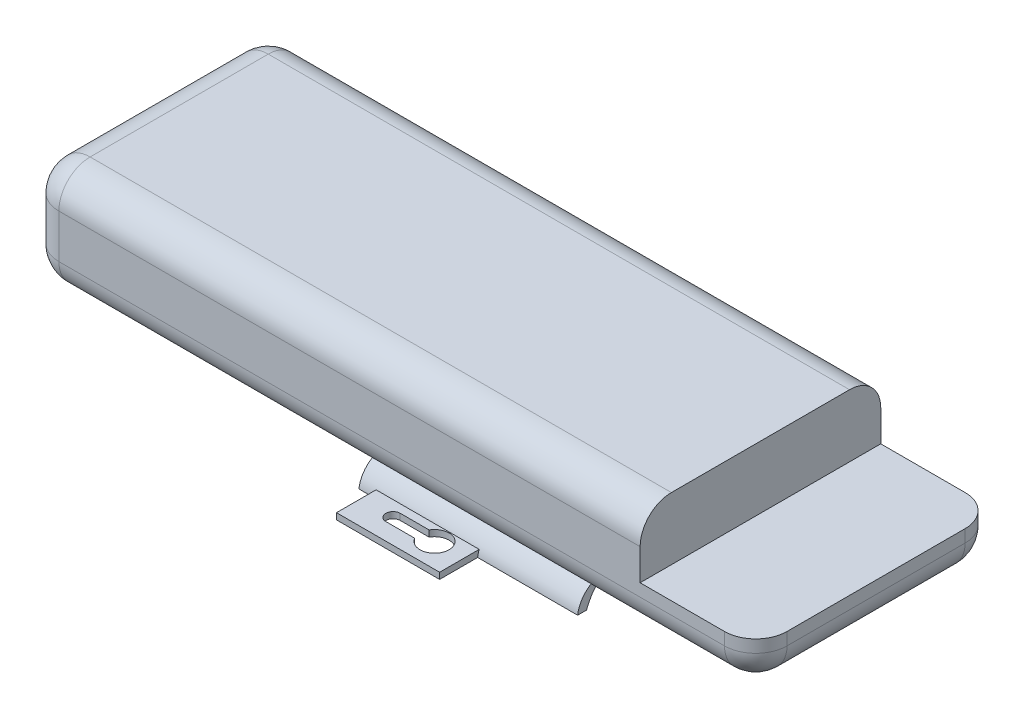
SolidWorks part; units mm, degrees
ref_plane "前视基准面" through (0, 0, 0) normal (0, 0, 1) x (1, 0, 0)
ref_plane "上视基准面" through (0, 0, 0) normal (0, 1, 0) x (1, 0, 0)
ref_plane "右视基准面" through (0, 0, 0) normal (1, 0, 0) x (0, 0, -1)
sketch "草图1" plane through (0, 0, 0) normal (0, 1, 0) x (1, 0, 0)
  line L1 (-116.5, 38.5) -> (116.5, 38.5)
  line L2 (-116.5, 38.5) -> (-116.5, -38.5)
  line L3 (-116.5, -38.5) -> (116.5, -38.5)
  line L4 (116.5, 38.5) -> (116.5, -38.5)
  line L5 (-116.5, 38.5) -> (116.5, -38.5) construction
  line L6 (-116.5, -38.5) -> (116.5, 38.5) construction
  point P0 (0, 0)
  dimension "D1" = 233
  dimension "D2" = 77
extrude "凸台-拉伸1" add sketch "草图1" along normal blind 34
fillet "圆角1" radius 10 12 edges at (-116.5, 17, -38.5) (-116.5, 34, 0) (-116.5, 17, 38.5) (-116.5, 0, 0) (116.5, 17, 38.5) (116.5, 34, 0) (116.5, 17, -38.5) (116.5, 0, 0) (0, 0, -38.5) (0, 34, -38.5) (0, 34, 38.5) (0, 0, 38.5)
sketch "草图4" plane through (116.5, 0, 0) normal (1, 0, 0) x (0, 0, -1)
  line L0 (0, 0) -> (0, -31.2961) construction
  line L1 (0, 0) -> (18.5, 0)
  line L2 (28.5, 0) -> (-28.5, 0) construction
  line L3 (18.5, 0) -> (18.5, -1.5721)
  line L4 (18.5, -25) -> (15.6612, -25)
  line L5 (0, 0) -> (0, -14)
  arc A0 (18.5, -1.5721) -> (14.0397, -18.3891) centre (18.5, -10.5721) ccw
  arc A1 (14.0397, -18.3891) -> (18.5, -25) centre (9.577, -26.2101) cw
  arc A2 (15.6612, -25) -> (0, -14) centre (0, -30.6488) ccw
  dimension "D1" = 11
  dimension "D3" = 9
  dimension "D2" = 37
  dimension "D4" = 18.5
  dimension "D5" = 25
extrude "凸台-拉伸2" add sketch "草图4" against normal blind 70 from offset 77 offset against normal yes
sketch "草图5" plane through (0, 34, 0) normal (0, 1, 0) x (1, 0, 0)
  line L0 (116.5, 28.5) -> (116.5, -28.5) construction
  line L1 (79.5, 62.5336) -> (139.2207, 62.5336)
  line L2 (79.5, 62.5336) -> (79.5, -62.1009)
  line L3 (79.5, -62.1009) -> (139.2207, -62.1009)
  line L4 (139.2207, 62.5336) -> (139.2207, -62.1009)
  dimension "D1" = 37
extrude "切除-拉伸1" cut sketch "草图5" against normal blind 20
mirror "镜向1" about plane through (-30.5, 0, 0) normal (0, 0, 1) of "凸台-拉伸2"
sketch "草图6" plane through (0, -25, 0) normal (0, -1, 0) x (1, 0, 0)
  line L0 (-30.5, 15.6612) -> (39.5, 15.6612) construction
  line L1 (-25.5, 15.6612) -> (7.5, 15.6612)
  line L2 (-25.5, 15.6612) -> (-25.5, 30.6612)
  line L3 (-25.5, 30.6612) -> (7.5, 30.6612)
  line L4 (7.5, 15.6612) -> (7.5, 30.6612)
  line L5 (-30.5, 15.6612) -> (-30.5, 18.5) construction
  dimension "D1" = 33
  dimension "D2" = 15
  dimension "D3" = 5
extrude "凸台-拉伸3" add sketch "草图6" against normal blind 2
sketch "草图7" plane through (0, -25, 0) normal (0, -1, 0) x (-1, 0, 0)
  line L0 (1.865, -22.9243) -> (15.1361, -22.9243) construction
  line L1 (5.9064, -20.6243) -> (15.1361, -20.6243)
  line L2 (5.9064, -25.2243) -> (15.1361, -25.2243)
  arc A0 (5.9064, -20.6243) -> (5.9064, -25.2243) centre (1.865, -22.9243) ccw
  arc A2 (15.1361, -25.2243) -> (15.1361, -20.6243) centre (15.1361, -22.9243) ccw
  point P3 (8.5005, -22.9243)
  dimension "D1" = 23
  dimension "D2" = 9.3
  dimension "D3" = 4.6
extrude "切除-拉伸2" cut sketch "草图7" against normal blind 2
mirror "镜向2" about plane through (0, 0, 0) normal (0, 0, 1) of "凸台-拉伸3", "切除-拉伸2"
